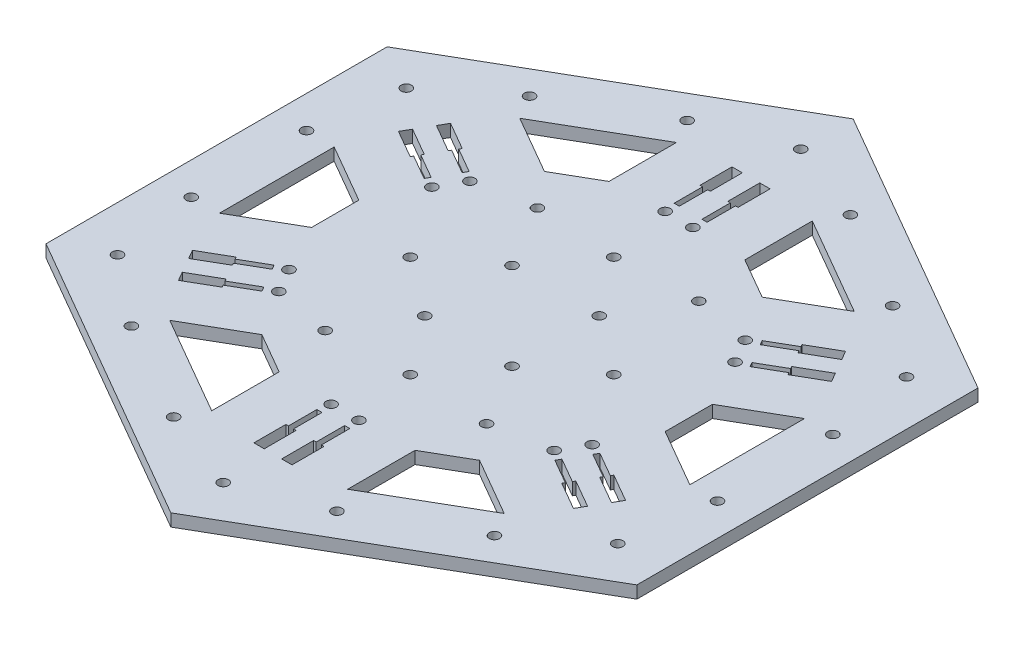
SolidWorks part; units mm, degrees
ref_plane "Front Plane" through (0, 0, 0) normal (0, 0, 1) x (1, 0, 0)
ref_plane "Top Plane" through (0, 0, 0) normal (0, 1, 0) x (1, 0, 0)
ref_plane "Right Plane" through (0, 0, 0) normal (1, 0, 0) x (0, 0, -1)
sketch "Sketch2" plane through (0, 0, 0) normal (0, 1, 0) x (1, 0, 0)
  line L1 (0, -117.3176) -> (101.6, -58.6588)
  line L2 (101.6, -58.6588) -> (101.6, 58.6588)
  line L3 (101.6, 58.6588) -> (0, 117.3176)
  line L4 (0, 117.3176) -> (-101.6, 58.6588)
  line L5 (-101.6, 58.6588) -> (-101.6, -58.6588)
  line L6 (-101.6, -58.6588) -> (0, -117.3176)
  circle A0 centre (0, 0) radius 101.6 construction
  dimension "D1" = 203.2
extrude "Boss-Extrude1" add sketch "Sketch2" along normal blind 4.25
sketch "Sketch3" plane through (0, 4.25, 0) normal (0, 1, 0) x (1, 0, 0)
  line L0 (-101.6, 0) -> (101.6, 0)
  line L1 (-101.6, 58.6588) -> (-101.6, -58.6588) construction
  line L2 (101.6, -58.6588) -> (101.6, 58.6588) construction
  line L3 (-50.8, 87.9882) -> (50.8, -87.9882)
  line L4 (0, 117.3176) -> (-101.6, 58.6588) construction
  line L5 (0, -117.3176) -> (101.6, -58.6588) construction
  line L6 (50.8, 87.9882) -> (-50.8, -87.9882)
  line L7 (101.6, 58.6588) -> (0, 117.3176) construction
  line L8 (-101.6, -58.6588) -> (0, -117.3176) construction
  line L10 (-23.365, -79.9024) -> (-23.365, -56.716)
  line L13 (-101.6, -58.6588) -> (0, 0)
  line L14 (-57.515, -60.1859) -> (-37.435, -48.5927)
  line L15 (-57.515, -60.1859) -> (-23.365, -79.9024)
  line L16 (-23.365, -56.716) -> (-37.435, -48.5927)
  line L17 (-80.88, 19.7165) -> (-60.8, 8.1234)
  line L18 (-80.88, -19.7165) -> (-80.88, 19.7165)
  line L19 (-80.88, -19.7165) -> (-60.8, -8.1234)
  line L20 (-60.8, 8.1234) -> (-60.8, -8.1234)
  line L21 (0, 0) -> (0, -117.3176)
  line L22 (-101.6, 58.6588) -> (101.6, -58.6588)
  line L23 (23.365, -79.9024) -> (23.365, -56.716)
  line L24 (57.515, -60.1859) -> (23.365, -79.9024)
  line L25 (57.515, -60.1859) -> (37.435, -48.5927)
  line L26 (23.365, -56.716) -> (37.435, -48.5927)
  line L27 (80.88, -19.7165) -> (60.8, -8.1234)
  line L28 (60.8, 8.1234) -> (60.8, -8.1234)
  line L29 (80.88, -19.7165) -> (80.88, 19.7165)
  line L30 (80.88, 19.7165) -> (60.8, 8.1234)
  line L31 (57.515, 60.1859) -> (37.435, 48.5927)
  line L32 (23.365, 79.9024) -> (57.515, 60.1859)
  line L33 (37.435, 48.5927) -> (23.365, 56.716)
  line L34 (23.365, 79.9024) -> (23.365, 56.716)
  line L35 (-23.365, 79.9024) -> (-23.365, 56.716)
  line L36 (-23.365, 79.9024) -> (-57.515, 60.1859)
  line L37 (-57.515, 60.1859) -> (-37.435, 48.5927)
  line L38 (-37.435, 48.5927) -> (-23.365, 56.716)
extrude "Cut-Extrude1" cut sketch "Sketch3" against normal blind 4.25 contours L6 L16 L14 L15 | L10 L16 L6 L15 | L26 L23 L24 L3 | L26 L3 L24 L25 | L27 L29 L0 L28 | L29 L30 L28 L0 | L33 L31 L32 L6 | L32 L34 L33 L6 | L37 L38 L3 L36 | L3 L38 L35 L36 | L17 L20 L19 L18
sketch "Sketch4" plane through (0, 4.25, 0) normal (0, 1, 0) x (1, 0, 0)
  line L0 (0, 0) -> (-101.6, 0) construction
  line L1 (-101.6, 58.6588) -> (-101.6, -58.6588) construction
  line L2 (-90.5, 0) -> (-90.5, 19.83) construction
  line L4 (-101.6, -58.6588) -> (101.6, 58.6588) construction
  line L5 (0, -117.3176) -> (0, 117.3176) construction
  line L6 (0, 0) -> (-101.6, 58.6588) construction
  point P8 (-90.5, -19.83)
  point P17 (-62.4233, 68.4603)
  point P20 (-28.0767, 88.2903)
  point P22 (-62.4233, -68.4603)
  point P23 (-28.0767, -88.2903)
  point P25 (28.0767, -88.2903)
  point P26 (62.4233, -68.4603)
  point P27 (90.5, -19.83)
  point P28 (90.5, 19.83)
  point P29 (62.4233, 68.4603)
  point P30 (28.0767, 88.2903)
  dimension "D1" = 11.1
hole_wizard "#37 (0.14015748) Diameter Hole1" positions "Sketch5" profile "Sketch6" hole size "#37" standard "ANSI Inch" end condition through all
sketch "Sketch5" plane through (0, 4.25, 0) normal (0, 1, 0) x (1, 0, 0)
  point P0 (62.4233, 68.4603)
  point P3 (90.5, 19.83)
  point P6 (90.5, -19.83)
  point P9 (62.4233, -68.4603)
  point P12 (28.0767, -88.2903)
  point P15 (-28.0767, -88.2903)
  point P18 (-62.4233, -68.4603)
  point P21 (-90.5, -19.83)
  point P24 (-90.5, 19.83)
  point P27 (-62.4233, 68.4603)
  point P30 (-28.0767, 88.2903)
  point P33 (28.0767, 88.2903)
sketch "Sketch6" plane through (62.4233, 4.25, -68.4603) normal (1, 0, 0) x (0, 0, 1)
  line L0 (0, 0) -> (0, 4.25)
  line L1 (0, 4.25) -> (1.78, 4.25)
  line L2 (1.78, 4.25) -> (1.78, 0)
  line L5 (1.78, 0) -> (0, 0)
  line L11 (0, -6.35) -> (0, 107.95) construction
  dimension "Thru Hole Dia." = 3.56
  dimension "Thru Hole Depth" = 4.25
sketch "Sketch7" plane through (0, 4.25, 0) normal (0, 1, 0) x (1, 0, 0)
  line L4 (-101.6, 58.6588) -> (101.6, -58.6588) construction
  line L5 (101.6, 58.6588) -> (-101.6, -58.6588) construction
  line L6 (0, -117.3176) -> (0, 117.3176) construction
  line L8 (101.6, -58.6588) -> (101.6, 58.6588) construction
  line L9 (0, -117.3176) -> (101.6, -58.6588) construction
  point P0 (86.0115, 49.6588)
  point P1 (86.0115, -49.6588)
  point P2 (0, 99.3176)
  point P3 (-86.0115, -49.6588)
  point P4 (-86.0115, 49.6588)
  point P5 (0, -99.3176)
  dimension "D1" = 18
  dimension "D2" = 18
  dimension "D3" = 18
  dimension "D4" = 15.5885
  dimension "D5" = 15.5885
  dimension "D6" = 18
  dimension "D7" = 18
  dimension "D8" = 18
hole_wizard "#37 (0.14015748) Diameter Hole2" positions "3DSketch1" profile "Sketch8" hole size "#37" standard "ANSI Inch" end condition through all
sketch3d "3DSketch1"
  point P0 (86.0115, 4.25, -49.6588)
  point P3 (86.0115, 4.25, 49.6588)
  point P6 (0, 4.25, 99.3176)
  point P9 (-86.0115, 4.25, 49.6588)
  point P12 (-86.0115, 4.25, -49.6588)
  point P15 (0, 4.25, -99.3176)
sketch "Sketch8" plane through (86.0115, 4.25, -49.6588) normal (1, 0, 0) x (0, 0, 1)
  line L0 (0, 0) -> (0, 4.25)
  line L1 (0, 4.25) -> (1.78, 4.25)
  line L2 (1.78, 4.25) -> (1.78, 0)
  line L5 (1.78, 0) -> (0, 0)
  line L11 (0, -6.35) -> (0, 107.95) construction
  dimension "Thru Hole Dia." = 3.56
  dimension "Thru Hole Depth" = 4.25
sketch "Sketch9" plane through (0, 4.25, 0) normal (0, 1, 0) x (1, 0, 0)
  line L0 (-101.6, 0) -> (101.6, 0) construction
  line L1 (-101.6, 58.6588) -> (-101.6, -58.6588) construction
  line L2 (101.6, -58.6588) -> (101.6, 58.6588) construction
  line L3 (0, 117.3176) -> (0, -117.3176) construction
  point P10 (15, 15)
  point P11 (15, -15)
  point P12 (-15, -15)
  point P13 (-15, 15)
  point P14 (27.75, 36.5)
  point P15 (27.75, -36.5)
  point P16 (-27.75, -36.5)
  point P17 (-27.75, 36.5)
  dimension "D1" = 30
  dimension "D2" = 15
  dimension "D3" = 30
  dimension "D4" = 15
  dimension "D5" = 30
  dimension "D6" = 30
  dimension "D7" = 15
  dimension "D8" = 15
  dimension "D9" = 73
  dimension "D10" = 55.5
  dimension "D11" = 73
  dimension "D12" = 36.5
  dimension "D13" = 36.5
  dimension "D14" = 27.75
hole_wizard "#37 (0.14015748) Diameter Hole3" positions "3DSketch2" profile "Sketch10" hole size "#37" standard "ANSI Inch" end condition through all
sketch3d "3DSketch2"
  point P0 (27.75, 4.25, -36.5)
  point P3 (-27.75, 4.25, -36.5)
  point P6 (-15, 4.25, -15)
  point P9 (15, 4.25, -15)
  point P12 (15, 4.25, 15)
  point P15 (-15, 4.25, 15)
  point P18 (-27.75, 4.25, 36.5)
  point P21 (27.75, 4.25, 36.5)
sketch "Sketch10" plane through (27.75, 4.25, -36.5) normal (1, 0, 0) x (0, 0, 1)
  line L0 (0, 0) -> (0, 4.25)
  line L1 (0, 4.25) -> (1.78, 4.25)
  line L2 (1.78, 4.25) -> (1.78, 0)
  line L5 (1.78, 0) -> (0, 0)
  line L11 (0, -6.35) -> (0, 107.95) construction
  dimension "Thru Hole Dia." = 3.56
  dimension "Thru Hole Depth" = 4.25
sketch "Sketch11" plane through (0, 4.25, 0) normal (0, 1, 0) x (1, 0, 0)
  line L0 (-69.6927, 43.7012) -> (-60.1665, 38.2012)
  line L2 (-60.1665, 38.2012) -> (-59.7217, 38.9716)
  line L77 (-58.8317, 40.5132) -> (-58.3867, 41.2839)
  line L78 (-58.3867, 41.2839) -> (-67.9129, 46.7839)
  line L79 (-68.008, 46.6192) -> (-69.788, 43.5362)
  line L80 (-59.7217, 38.9716) -> (-51.2532, 34.0823)
  line L81 (-58.8317, 40.5132) -> (-50.3632, 35.6239)
  line L82 (-74.477, 35.4245) -> (-64.9507, 29.9245)
  line L83 (-64.9507, 29.9245) -> (-64.5059, 30.6949)
  line L84 (-63.6157, 32.2368) -> (-63.1707, 33.0075)
  line L85 (-63.1707, 33.0075) -> (-72.697, 38.5075)
  line L86 (-72.793, 38.3413) -> (-74.573, 35.2582)
  line L87 (-64.5059, 30.6949) -> (-56.0374, 25.8056)
  line L88 (-63.6157, 32.2368) -> (-55.1472, 27.3475)
  line L89 (-50.3632, 35.6239) -> (-51.2532, 34.0823)
  line L90 (-55.1472, 27.3475) -> (-56.0374, 25.8056)
  circle A9 centre (-47.344, 32.8531) radius 1.78
  circle A10 centre (-52.1283, 24.5764) radius 1.78
  dimension "D9" = 11
  dimension "D10" = 11
  dimension "D13" = 3.56
  dimension "D14" = 3.56
  dimension "D5" = 0.89
  dimension "D7" = 0.8896
  dimension "D11" = 11
  dimension "D12" = 11
  dimension "D45" = 0.89
  dimension "D46" = 4
  dimension "D88" = 3.9091
  dimension "D89" = 4.0978
sketch "Sketch13" plane through (0, 4.25, 0) normal (0, 1, 0) x (1, 0, 0)
  line L0 (-50.3632, 35.6239) -> (-51.2532, 34.0823)
  line L1 (-51.2532, 34.0823) -> (-59.7217, 38.9716)
  line L2 (-59.7217, 38.9716) -> (-60.1665, 38.2012)
  line L5 (-67.9129, 46.7839) -> (-58.3867, 41.2839)
  line L6 (-58.3867, 41.2839) -> (-58.8317, 40.5132)
  line L7 (-58.8317, 40.5132) -> (-50.3632, 35.6239)
  line L8 (-55.1472, 27.3475) -> (-56.0374, 25.8056)
  line L9 (-56.0374, 25.8056) -> (-64.5059, 30.6949)
  line L10 (-64.5059, 30.6949) -> (-64.9507, 29.9245)
  line L11 (-64.9507, 29.9245) -> (-74.477, 35.4245)
  line L12 (-74.477, 35.4245) -> (-72.697, 38.5075)
  line L13 (-72.697, 38.5075) -> (-63.1707, 33.0075)
  line L14 (-63.1707, 33.0075) -> (-63.6157, 32.2368)
  line L15 (-63.6157, 32.2368) -> (-55.1472, 27.3475)
  line L16 (-60.1665, 38.2012) -> (-69.6927, 43.7012)
  line L17 (-69.6927, 43.7012) -> (-67.9129, 46.7839)
  line L18 (5.6696, 61.4277) -> (3.8896, 61.4277)
  line L19 (3.8896, 61.4277) -> (3.8896, 71.2063)
  line L20 (3.8896, 71.2063) -> (3, 71.2063)
  line L21 (6.5596, 82.2063) -> (6.5596, 71.2063)
  line L22 (6.5596, 71.2063) -> (5.6696, 71.2063)
  line L23 (5.6696, 71.2063) -> (5.6696, 61.4277)
  line L24 (-3.89, 61.4326) -> (-5.6704, 61.4326)
  line L25 (-5.6704, 61.4326) -> (-5.6704, 71.2112)
  line L26 (-5.6704, 71.2112) -> (-6.56, 71.2112)
  line L27 (-6.56, 71.2112) -> (-6.56, 82.2112)
  line L28 (-6.56, 82.2112) -> (-3, 82.2112)
  line L29 (-3, 82.2112) -> (-3, 71.2112)
  line L30 (-3, 71.2112) -> (-3.89, 71.2112)
  line L31 (-3.89, 71.2112) -> (-3.89, 61.4326)
  line L32 (3, 71.2063) -> (3, 82.2063)
  line L33 (3, 82.2063) -> (6.5596, 82.2063)
  line L34 (56.0327, 25.8038) -> (55.1428, 27.3454)
  line L35 (55.1428, 27.3454) -> (63.6113, 32.2347)
  line L36 (63.6113, 32.2347) -> (63.1665, 33.0051)
  line L37 (74.4725, 35.4224) -> (64.9463, 29.9224)
  line L38 (64.9463, 29.9224) -> (64.5013, 30.6931)
  line L39 (64.5013, 30.6931) -> (56.0327, 25.8038)
  line L40 (51.2572, 34.0851) -> (50.367, 35.627)
  line L41 (50.367, 35.627) -> (58.8355, 40.5163)
  line L42 (58.8355, 40.5163) -> (58.3907, 41.2867)
  line L43 (58.3907, 41.2867) -> (67.917, 46.7867)
  line L44 (67.917, 46.7867) -> (69.697, 43.7037)
  line L45 (69.697, 43.7037) -> (60.1707, 38.2037)
  line L46 (60.1707, 38.2037) -> (59.7257, 38.9744)
  line L47 (59.7257, 38.9744) -> (51.2572, 34.0851)
  line L48 (63.1665, 33.0051) -> (72.6927, 38.5051)
  line L49 (72.6927, 38.5051) -> (74.4725, 35.4224)
  line L50 (50.3632, -35.6239) -> (51.2532, -34.0823)
  line L51 (51.2532, -34.0823) -> (59.7217, -38.9716)
  line L52 (59.7217, -38.9716) -> (60.1665, -38.2012)
  line L53 (67.9129, -46.7839) -> (58.3867, -41.2839)
  line L54 (58.3867, -41.2839) -> (58.8317, -40.5132)
  line L55 (58.8317, -40.5132) -> (50.3632, -35.6239)
  line L56 (55.1472, -27.3475) -> (56.0374, -25.8056)
  line L57 (56.0374, -25.8056) -> (64.5059, -30.6949)
  line L58 (64.5059, -30.6949) -> (64.9507, -29.9245)
  line L59 (64.9507, -29.9245) -> (74.477, -35.4245)
  line L60 (74.477, -35.4245) -> (72.697, -38.5075)
  line L61 (72.697, -38.5075) -> (63.1707, -33.0075)
  line L62 (63.1707, -33.0075) -> (63.6157, -32.2368)
  line L63 (63.6157, -32.2368) -> (55.1472, -27.3475)
  line L64 (60.1665, -38.2012) -> (69.6927, -43.7012)
  line L65 (69.6927, -43.7012) -> (67.9129, -46.7839)
  line L66 (-5.6696, -61.4277) -> (-3.8896, -61.4277)
  line L67 (-3.8896, -61.4277) -> (-3.8896, -71.2063)
  line L68 (-3.8896, -71.2063) -> (-3, -71.2063)
  line L69 (-6.5596, -82.2063) -> (-6.5596, -71.2063)
  line L70 (-6.5596, -71.2063) -> (-5.6696, -71.2063)
  line L71 (-5.6696, -71.2063) -> (-5.6696, -61.4277)
  line L72 (3.89, -61.4326) -> (5.6704, -61.4326)
  line L73 (5.6704, -61.4326) -> (5.6704, -71.2112)
  line L74 (5.6704, -71.2112) -> (6.56, -71.2112)
  line L75 (6.56, -71.2112) -> (6.56, -82.2112)
  line L76 (6.56, -82.2112) -> (3, -82.2112)
  line L77 (3, -82.2112) -> (3, -71.2112)
  line L78 (3, -71.2112) -> (3.89, -71.2112)
  line L79 (3.89, -71.2112) -> (3.89, -61.4326)
  line L80 (-3, -71.2063) -> (-3, -82.2063)
  line L81 (-3, -82.2063) -> (-6.5596, -82.2063)
  line L82 (-56.0327, -25.8038) -> (-55.1428, -27.3454)
  line L83 (-55.1428, -27.3454) -> (-63.6113, -32.2347)
  line L84 (-63.6113, -32.2347) -> (-63.1665, -33.0051)
  line L85 (-74.4725, -35.4224) -> (-64.9463, -29.9224)
  line L86 (-64.9463, -29.9224) -> (-64.5013, -30.6931)
  line L87 (-64.5013, -30.6931) -> (-56.0327, -25.8038)
  line L88 (-51.2572, -34.0851) -> (-50.367, -35.627)
  line L89 (-50.367, -35.627) -> (-58.8355, -40.5163)
  line L90 (-58.8355, -40.5163) -> (-58.3907, -41.2867)
  line L91 (-58.3907, -41.2867) -> (-67.917, -46.7867)
  line L92 (-67.917, -46.7867) -> (-69.697, -43.7037)
  line L93 (-69.697, -43.7037) -> (-60.1707, -38.2037)
  line L94 (-60.1707, -38.2037) -> (-59.7257, -38.9744)
  line L95 (-59.7257, -38.9744) -> (-51.2572, -34.0851)
  line L96 (-63.1665, -33.0051) -> (-72.6927, -38.5051)
  line L97 (-72.6927, -38.5051) -> (-74.4725, -35.4224)
  circle A0 centre (-47.344, 32.8531) radius 1.78
  circle A1 centre (-52.1283, 24.5764) radius 1.78
  circle A2 centre (4.7796, 57.4277) radius 1.78
  circle A3 centre (-4.7804, 57.4326) radius 1.78
  circle A4 centre (52.1237, 24.5746) radius 1.78
  circle A5 centre (47.3479, 32.8562) radius 1.78
  circle A6 centre (47.344, -32.8531) radius 1.78
  circle A7 centre (52.1283, -24.5764) radius 1.78
  circle A8 centre (-4.7796, -57.4277) radius 1.78
  circle A9 centre (4.7804, -57.4326) radius 1.78
  circle A10 centre (-52.1237, -24.5746) radius 1.78
  circle A11 centre (-47.3479, -32.8562) radius 1.78
  dimension "D1" = 6
extrude "Cut-Extrude7" cut sketch "Sketch13" against normal blind 10
sketch "Sketch14" plane through (0, 4.25, 0) normal (0, 1, 0) x (1, 0, 0)
  point P7 (35, 0)
  point P8 (0, 35)
  point P9 (0, -35)
  point P10 (-35, 0)
  point P12 (35, 0)
  point P13 (0, -35)
  point P14 (-35, 0)
  point P15 (35, 0)
  point P16 (0, -35)
  point P17 (-35, 0)
  dimension "D1" = 35
  dimension "D2" = 4
  dimension "D3" = 4
  dimension "D4" = 4
hole_wizard "#37 (0.14015748) Diameter Hole5" positions "3DSketch5" profile "Sketch17" hole size "#37" standard "ANSI Inch" end condition through all
sketch3d "3DSketch5"
  point P0 (0, 4.25, -35)
  point P3 (35, 4.25, 0)
  point P6 (0, 4.25, 35)
  point P9 (-35, 4.25, 0)
sketch "Sketch17" plane through (0, 4.25, -35) normal (1, 0, 0) x (0, 0, 1)
  line L0 (0, 0) -> (0, 4.25)
  line L1 (0, 4.25) -> (1.78, 4.25)
  line L2 (1.78, 4.25) -> (1.78, 0)
  line L5 (1.78, 0) -> (0, 0)
  line L11 (0, -6.35) -> (0, 107.95) construction
  dimension "Thru Hole Dia." = 3.56
  dimension "Thru Hole Depth" = 4.25
